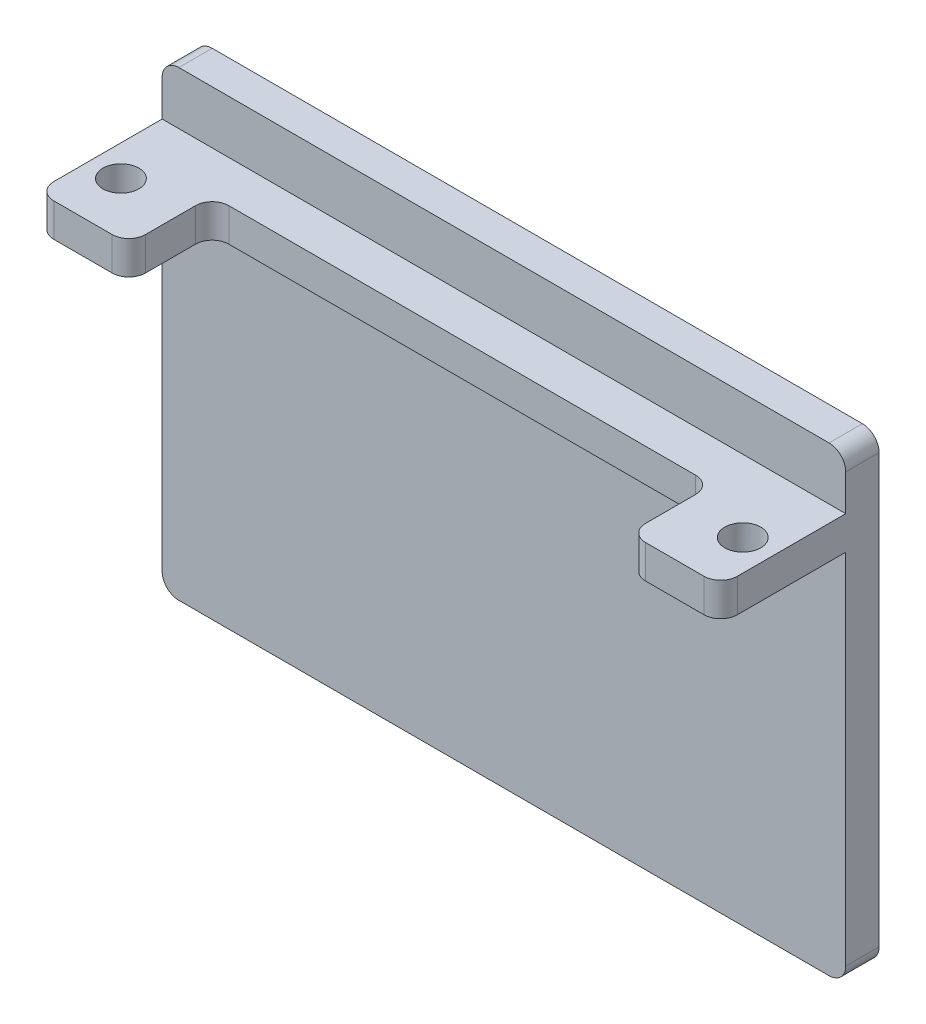
SolidWorks part; units mm, degrees
ref_plane "Front Plane" through (0, 0, 0) normal (0, 0, 1) x (1, 0, 0)
ref_plane "Top Plane" through (0, 0, 0) normal (0, 1, 0) x (1, 0, 0)
ref_plane "Right Plane" through (0, 0, 0) normal (1, 0, 0) x (0, 0, -1)
sketch "Sketch1" plane through (0, 0, 0) normal (0, 0, 1) x (1, 0, 0)
  line L1 (0, 0) -> (82, 0)
  line L2 (0, 0) -> (0, -49)
  line L3 (0, -49) -> (82, -49)
  line L4 (82, 0) -> (82, -49)
  line L5 (0, 0) -> (82, -49) construction
  line L6 (0, -49) -> (82, 0) construction
  point P4 (41, -24.5)
  dimension "D1" = 82
  dimension "D2" = 49
extrude "Boss-Extrude1" add sketch "Sketch1" along normal blind 4
sketch "Sketch2" plane through (0, 0, 4) normal (0, 0, 1) x (1, 0, 0)
  line L0 (82, -49) -> (82, 0) construction
  line L1 (0, 0) -> (82, 0)
  line L2 (0, 0) -> (0, -4)
  line L3 (0, -4) -> (82, -4)
  line L4 (82, 0) -> (82, -4)
  line L5 (0, 0) -> (82, -4) construction
  line L6 (0, -4) -> (82, 0) construction
  point P4 (41, -2)
  dimension "D1" = 4
extrude "Boss-Extrude2" add sketch "Sketch2" along normal blind 15
sketch "Sketch3" plane through (0, 0, 0) normal (0, 1, 0) x (1, 0, 0)
  line L0 (41, -19) -> (41, 0) construction
  line L1 (82, -19) -> (0, -19) construction
  line L2 (82, 0) -> (0, 0) construction
  line L3 (0, -12.65) -> (82, -12.65) construction
  line L4 (0, -19) -> (0, 0) construction
  line L5 (82, -19) -> (82, 0) construction
  circle A0 centre (3.7048, -12.65) radius 2.159
  circle A1 centre (78.2952, -12.65) radius 2.159
  point P16 (0, 0)
  dimension "D1" = 74.5903
  dimension "D2" = 4.318
  dimension "D3" = 6.35
extrude "Cut-Extrude1" cut sketch "Sketch3" against normal through all
sketch "Sketch4" plane through (0, 0, 0) normal (0, 1, 0) x (1, 0, 0)
  line L0 (82, -19) -> (82, 0) construction
  line L1 (0, 0) -> (82, 0)
  line L2 (0, 0) -> (0, -4)
  line L3 (0, -4) -> (82, -4)
  line L4 (82, 0) -> (82, -4)
  line L5 (0, 0) -> (82, -4) construction
  line L6 (0, -4) -> (82, 0) construction
  point P4 (41, -2)
  dimension "D1" = 4
extrude "Boss-Extrude3" add sketch "Sketch4" along normal blind 6.35
sketch "Sketch5" plane through (0, 0, 19) normal (0, 0, 1) x (1, 0, 0)
  line L0 (41, 0) -> (41, -4) construction
  line L1 (82, 0) -> (0, 0) construction
  line L2 (0, -4) -> (82, -4) construction
  line L4 (11, -4) -> (71, -4)
  line L5 (11, -4) -> (11, 0)
  line L6 (11, 0) -> (71, 0)
  line L7 (71, -4) -> (71, 0)
  line L8 (11, -4) -> (71, 0) construction
  line L9 (11, 0) -> (71, -4) construction
  point P6 (41, -2)
  dimension "D1" = 60
extrude "Cut-Extrude2" cut sketch "Sketch5" against normal blind 10
fillet "Fillet1" radius 2 10 edges at (0, -49, 2) (82, -49, 2) (82, 6.35, 2) (0, 6.35, 2) (0, -2, 19) (82, -2, 19) (71, -2, 19) (71, -2, 9) (11, -2, 19) (11, -2, 9)
